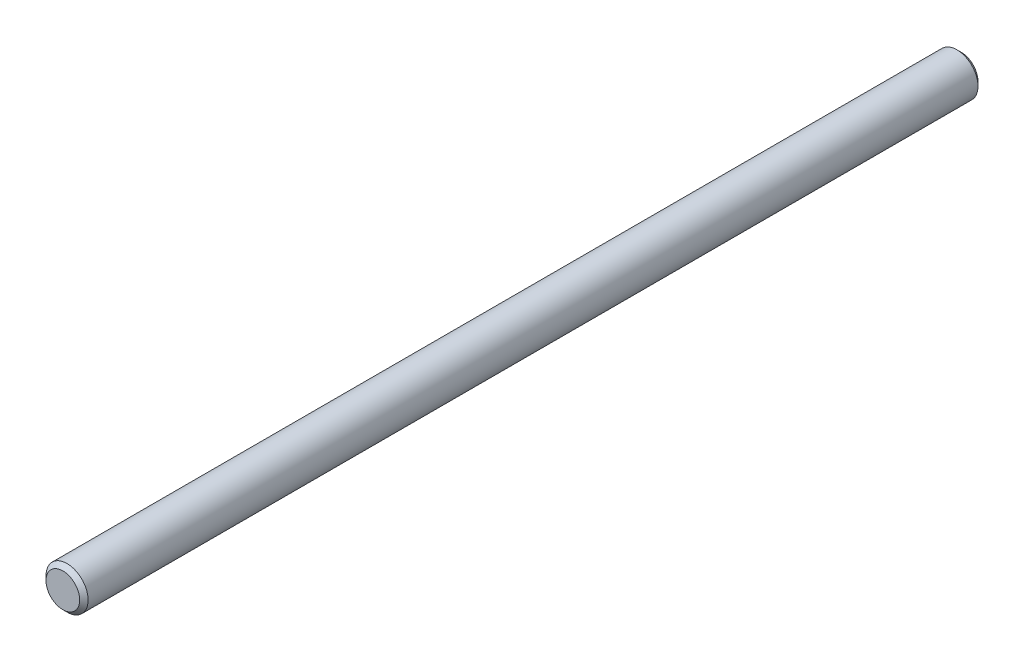
SolidWorks part; units mm, degrees
ref_plane "Front" through (0, 0, 0) normal (0, 0, 1) x (1, 0, 0)
ref_plane "Top" through (0, 0, 0) normal (0, 1, 0) x (1, 0, 0)
ref_plane "Right" through (0, 0, 0) normal (1, 0, 0) x (0, 0, -1)
sketch "Sketch1" plane through (0, 0, 0) normal (0, 0, 1) x (1, 0, 0)
  circle A0 centre (0, 0) radius 2.3813
  dimension "dia" = 4.7625
extrude "Extrude1" add sketch "Sketch1" along normal mid plane 101.6
sketch "Sketch2" plane through (0, 0, 0) normal (1, 0, 0) x (0, 0, -1)
  point P0 (-50.8, 2.3813)
  point P1 (50.8, 2.3813)
chamfer "Chamfer1" distance 0.4763 angle 45 2 edges at (2.3813, 0, -50.8) (2.3813, 0, 50.8)
equation "\"D1@Chamfer1\" = \"dia@Sketch1\" * .1"
